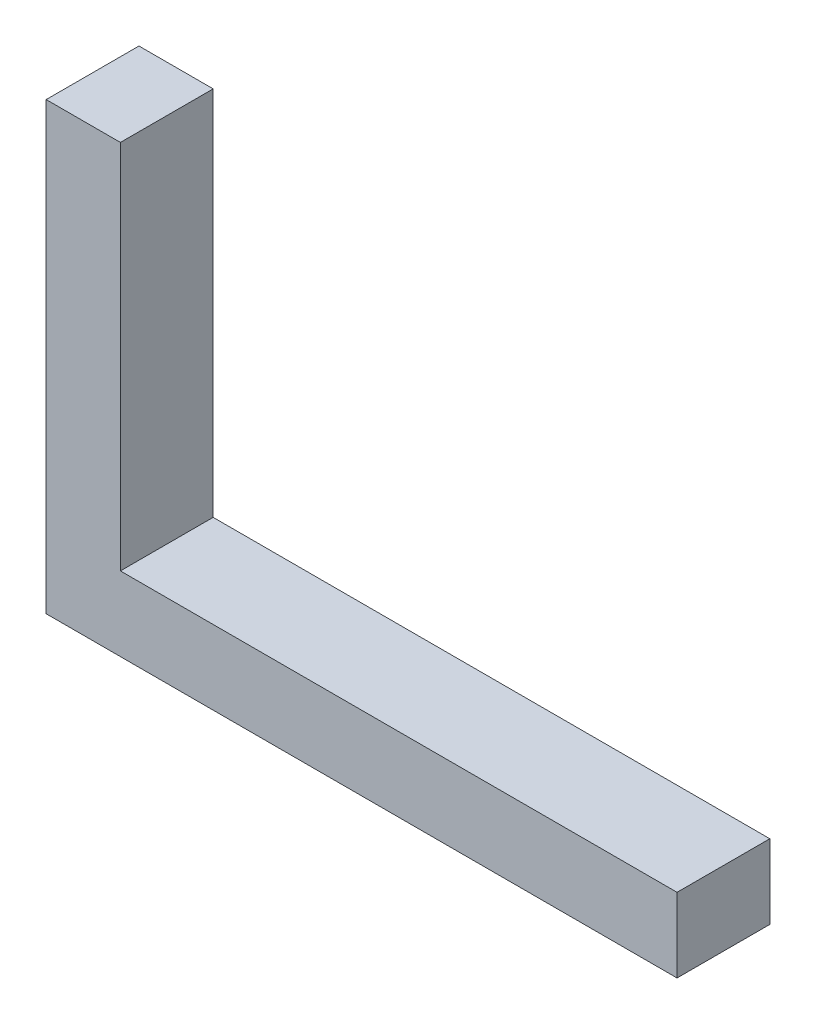
SolidWorks part; units mm, degrees
ref_plane "Front Plane" through (0, 0, 0) normal (0, 0, 1) x (1, 0, 0)
ref_plane "Top Plane" through (0, 0, 0) normal (0, 1, 0) x (1, 0, 0)
ref_plane "Right Plane" through (0, 0, 0) normal (1, 0, 0) x (0, 0, -1)
sketch "Sketch1" plane through (0, 0, 0) normal (0, 0, 1) x (1, 0, 0)
  line L0 (0, 24) -> (0, 0)
  line L1 (0, 0) -> (34, 0)
  line L2 (34, 0) -> (34, 4)
  line L3 (34, 4) -> (4, 4)
  line L4 (4, 4) -> (4, 24)
  line L5 (4, 24) -> (0, 24)
  point P3 (0, 0)
  dimension "D1" = 4
  dimension "D2" = 4
  dimension "D3" = 30
  dimension "D4" = 20
  dimension "D5" = 20
  dimension "D6" = 30
extrude "Boss-Extrude1" add sketch "Sketch1" along normal blind 5
